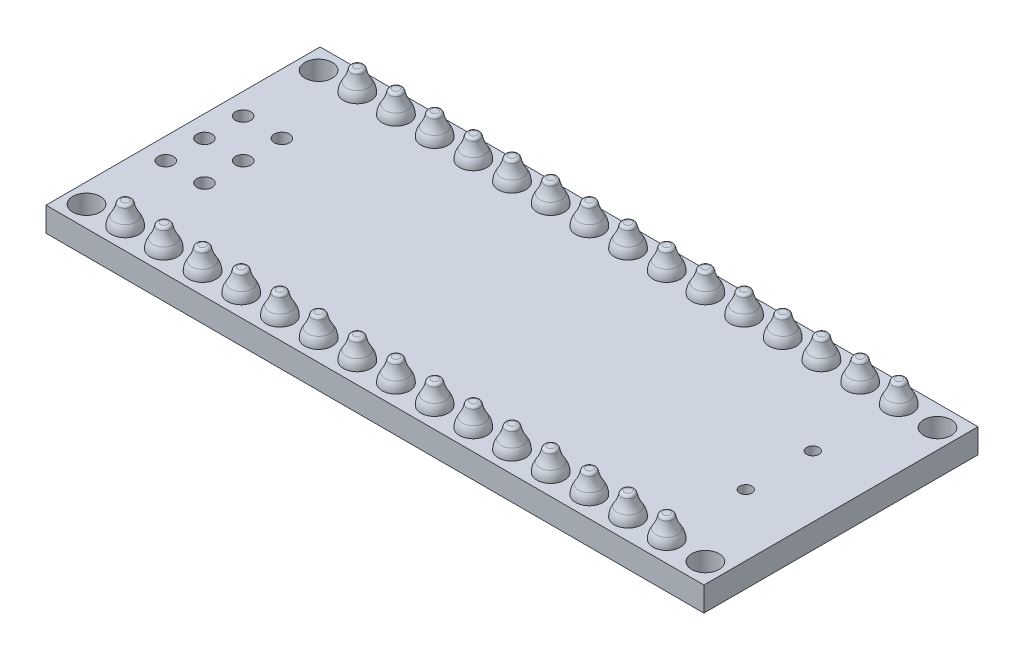
SolidWorks part; units mm, degrees
material "普通碳钢"
ref_plane "Front Plane" through (0, 0, 0) normal (0, 0, 1) x (1, 0, 0)
ref_plane "Top Plane" through (0, 0, 0) normal (0, 1, 0) x (1, 0, 0)
ref_plane "Right Plane" through (0, 0, 0) normal (1, 0, 0) x (0, 0, -1)
sketch "Sketch1" plane through (0, 0, 0) normal (0, 1, 0) x (1, 0, 0)
  line L0 (0, 7.62) -> (-3.82, 7.62) construction
  line L1 (-3.82, 16.62) -> (39.38, 16.62)
  line L2 (-3.82, 16.62) -> (-3.82, -1.38)
  line L3 (-3.82, -1.38) -> (39.38, -1.38)
  line L4 (39.38, 16.62) -> (39.38, -1.38)
  line L5 (0, 0) -> (35.56, 0) construction
  line L6 (0, 0) -> (0, 15.24) construction
  line L7 (0, 15.24) -> (35.56, 15.24) construction
  line L8 (35.56, 0) -> (35.56, 15.24) construction
  line L10 (35.56, 7.62) -> (39.38, 7.62) construction
  dimension "D1" = 43.2
  dimension "D2" = 18
  dimension "D3" = 15.24
  dimension "D4" = 35.56
extrude "Boss-Extrude2" add sketch "Sketch1" along normal blind 1.6
sketch "Sketch2" plane through (0, 0, 0) normal (0, 1, 0) x (1, 0, 0)
  line L0 (0, -0.88) -> (0, 0.88) construction
  line L2 (-0.88, 0) -> (0.88, 0) construction
  circle A0 centre (0, 0) radius 0.45
  circle A1 centre (0, 15.24) radius 0.45
  dimension "D1" = 0.9
  dimension "D2" = 15.24
extrude "Cut-Extrude2" cut sketch "Sketch2" along normal blind 1.6
pattern_linear "LPattern1" count 15 spacing 2.54 along (1, 0, 0) of "Cut-Extrude2"
sketch "Sketch3" plane through (0, 0, 0) normal (0, 1, 0) x (1, 0, 0)
  line L1 (-0.88, 0) -> (0.88, 0) construction
  line L2 (0, -0.88) -> (0, 0.88) construction
  circle A0 centre (0.127, 10.16) radius 0.5
  circle A1 centre (-2.413, 10.16) radius 0.5
  circle A2 centre (-2.413, 7.62) radius 0.5
  circle A3 centre (-2.413, 5.08) radius 0.5
  circle A4 centre (0.127, 5.08) radius 0.5
  circle A5 centre (0.127, 7.62) radius 0.5
  dimension "D1" = 1
  dimension "D5" = 7.62
  dimension "D2" = 2.54
  dimension "D3" = 2.54
  dimension "D4" = 2.54
  dimension "D6" = 2.54
  dimension "D7" = 0.127
extrude "Cut-Extrude4" cut sketch "Sketch3" along normal blind 1.6
sketch "Sketch4" plane through (0, 0, 0) normal (0, 1, 0) x (1, 0, 0)
  line L0 (-0.88, 0) -> (0.88, 0) construction
  line L1 (0, -0.88) -> (0, 0.88) construction
  circle A0 centre (38.1, 15.24) radius 0.9
  circle A1 centre (38.1, 0) radius 0.9
  circle A2 centre (-2.54, 0) radius 0.9
  circle A3 centre (-2.54, 15.24) radius 0.9
  dimension "D3" = 1.8
  dimension "D1" = 40.64
  dimension "D2" = 2.54
  dimension "D4" = 15.24
  dimension "D5" = 15.24
extrude "Cut-Extrude5" cut sketch "Sketch4" along normal blind 1.6
sketch "Sketch5" plane through (0, 1.6, 0) normal (0, 1, 0) x (1, 0, 0)
  circle A0 centre (38.1, 15.24) radius 0.9
  circle A1 centre (38.1, 15.24) radius 1.275
  circle A2 centre (38.1, 15.24) radius 0.9 construction
  circle A3 centre (38.1, 0) radius 0.9
  circle A4 centre (38.1, 0) radius 0.9 construction
  circle A5 centre (38.1, 0) radius 1.275
  circle A6 centre (-2.54, 15.24) radius 0.9
  circle A7 centre (-2.54, 15.24) radius 1.275
  circle A8 centre (-2.54, 0) radius 0.9
  circle A9 centre (-2.54, 0) radius 1.275
  circle A10 centre (-2.54, 15.24) radius 0.9 construction
  circle A11 centre (-2.54, 0) radius 0.9 construction
  dimension "D1" = 2.55
extrude "Boss-Extrude3" [suppressed] add sketch "Sketch5" along normal blind 0.1
sketch "Sketch6" plane through (0, 0, 0) normal (1, 0, 0) x (0, 0, -1)
  line L0 (0, 1.6) -> (0.9, 1.6)
  line L1 (-1.38, 1.6) -> (16.62, 1.6) construction
  line L2 (0.2252, 3.1) -> (0, 3.1)
  line L3 (0, 2.53) -> (0, -2.53) construction
  line L4 (0, 3.1) -> (0, 1.6)
  line L5 (0, 1.3722) -> (0, 3.4408) construction
  arc A0 (0.9, 1.6) -> (0.7139, 2.2122) centre (-0.2, 1.6) ccw
  arc A1 (0.7139, 2.2122) -> (0.4221, 2.9352) centre (2.2924, 3.2697) cw
  arc A2 (0.4221, 2.9352) -> (0.2252, 3.1) centre (0.2252, 2.9) ccw
  point P16 (0.4, 3.1)
  dimension "D4" = 1.1
  dimension "D5" = 1.9
  dimension "D6" = 0.2
  dimension "D1" = 1.5
  dimension "D2" = 0.8
  dimension "D3" = 1.8
revolve "Revolve1" add sketch "Sketch6" angle 360 about L5
pattern_linear "LPattern2" count 2 spacing 15.24 along (0, 0, -1) count 15 spacing 2.54 along (1, 0, 0) of "Revolve1"
ref_plane "Plane3" through (0, 0, -5.08) normal (0, 0, 1) x (1, 0, 0)
sketch "Sketch7" plane through (0, 0, -5.08) normal (0, 0, 1) x (1, 0, 0)
  line L0 (0.127, 3.889) -> (0.127, -2.5597) construction
  line L2 (0, -1.705) -> (0, 1.705) construction
  line L3 (0.127, 0) -> (1.027, 0)
  line L4 (9.9, 0) -> (-9.9, 0) construction
  line L5 (0.127, 0) -> (0.127, -1.5)
  line L6 (0.127, -1.5) -> (0.3395, -1.5)
  arc A0 (0.538, -1.325) -> (0.807, -0.66) centre (1.927, -1.5) cw
  arc A1 (0.807, -0.66) -> (1.027, 0) centre (-0.073, 0) ccw
  arc A2 (0.3395, -1.5) -> (0.538, -1.325) centre (0.3395, -1.3) ccw
  point P16 (0.527, -1.5)
  dimension "D5" = 1.1
  dimension "D6" = 0.2
  dimension "D1" = 0.127
  dimension "D2" = 1.5
  dimension "D3" = 0.8
  dimension "D4" = 1.8
revolve "Revolve2" add sketch "Sketch7" angle 360 about L0
pattern_linear "LPattern3" count 2 spacing 2.54 along (-1, 0, 0) count 3 spacing 2.54 along (0, 0, -1) of "Revolve2"
sketch "Sketch8" plane through (0, 0, 0) normal (0, -1, 0) x (1, 0, 0)
  circle A0 centre (38.1, 0) radius 0.9
  circle A1 centre (38.1, 0) radius 1.275
  circle A2 centre (38.1, -15.24) radius 1.275
  circle A3 centre (38.1, -15.24) radius 0.9
  circle A4 centre (38.1, -15.24) radius 0.9 construction
  circle A5 centre (38.1, 0) radius 0.9 construction
  circle A6 centre (-2.54, 0) radius 0.9
  circle A7 centre (-2.54, 0) radius 1.275
  circle A8 centre (-2.54, -15.24) radius 0.9
  circle A9 centre (-2.54, -15.24) radius 1.275
  circle A10 centre (-2.54, 0) radius 0.9 construction
  circle A11 centre (-2.54, -15.24) radius 0.9 construction
  dimension "D1" = 2.55
extrude "Boss-Extrude4" [suppressed] add sketch "Sketch8" along normal blind 0.1
sketch "Sketch9" plane through (0, 0, 0) normal (0, 1, 0) x (1, 0, 0)
  line L0 (-2.53, 0) -> (2.53, 0) construction
  line L1 (39.38, -1.38) -> (39.38, 16.62) construction
  circle A0 centre (35.33, 5.42) radius 0.4
  circle A1 centre (35.33, 9.82) radius 0.4
  dimension "D1" = 0.8
  dimension "D2" = 4.4
  dimension "D3" = 5.42
  dimension "D4" = 4.05
extrude "Cut-Extrude6" cut sketch "Sketch9" along normal blind 10
